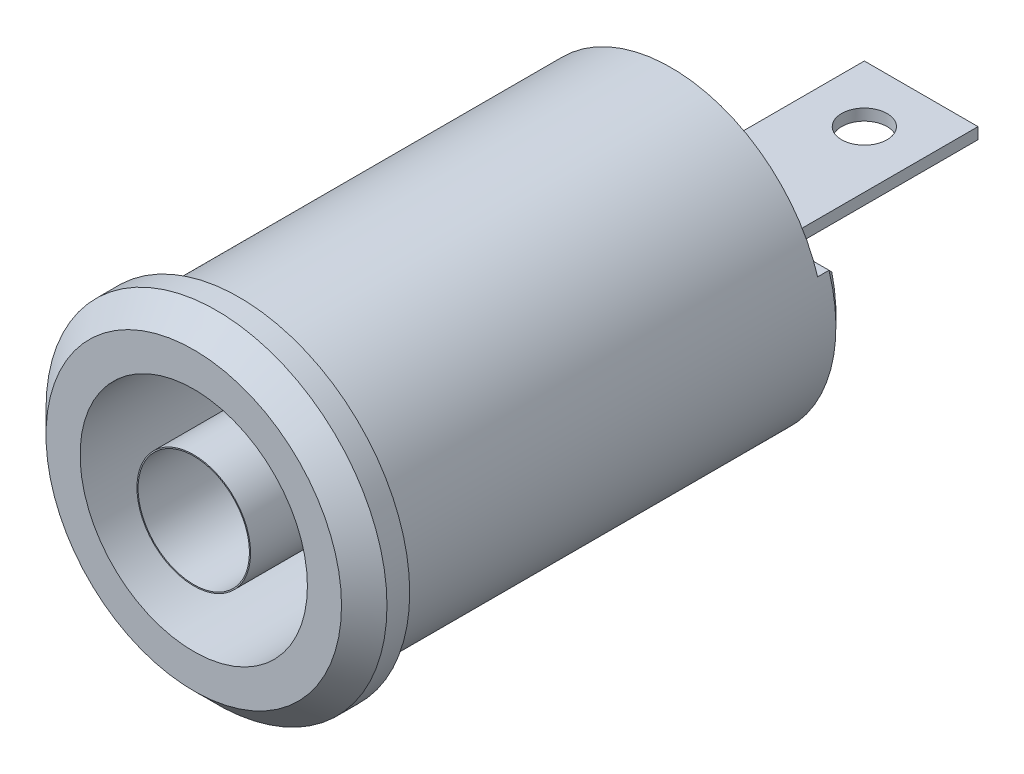
SolidWorks part; units mm, degrees
ref_plane "Plan de face" through (0, 0, 0) normal (0, 0, 1) x (1, 0, 0)
ref_plane "Plan de dessus" through (0, 0, 0) normal (0, 1, 0) x (1, 0, 0)
ref_plane "Plan de droite" through (0, 0, 0) normal (1, 0, 0) x (0, 0, -1)
sketch "Esquisse1" plane through (0, 0, 0) normal (0, 0, 1) x (1, 0, 0)
  circle A0 centre (0, 0) radius 7.5
  dimension "D1" = 15
extrude "Extrusion1" add sketch "Esquisse1" against normal blind 32
sketch "Esquisse2" plane through (0, 0, 0) normal (0, 0, 1) x (1, 0, 0)
  circle A0 centre (0, 0) radius 5
  circle A1 centre (0, 0) radius 2.5
  circle A2 centre (0, 0) radius 2.45
  dimension "D1" = 10
  dimension "D2" = 5
  dimension "D3" = 4.9
extrude "Extrusion3" cut sketch "Esquisse2" against normal blind 18 contours A0 A1 | A2
sketch "Esquisse3" plane through (0, 0, -32) normal (0, 0, -1) x (-1, 0, 0)
  circle A0 centre (0, 0) radius 6.75
  dimension "D1" = 13.5
extrude "Extrusion5" cut sketch "Esquisse3" against normal blind 30 flip side to cut
sketch "Esquisse4" plane through (0, 0, -32) normal (0, 0, -1) x (-1, 0, 0)
  line L0 (0, 7.9888) -> (0, -8.2444) construction
  line L1 (-2.5, 0.25) -> (2.5, 0.25)
  line L2 (-2.5, 0.25) -> (-2.5, -0.25)
  line L3 (-2.5, -0.25) -> (2.5, -0.25)
  line L4 (2.5, 0.25) -> (2.5, -0.25)
  line L5 (9.1392, 0) -> (-9.0881, 0) construction
  dimension "D1" = 0.25
  dimension "D2" = 0.25
  dimension "D3" = 2.5
  dimension "D4" = 2.5
extrude "Extrusion6" cut sketch "Esquisse4" against normal blind 10 flip side to cut
sketch "Esquisse5" plane through (0, 0, -22) normal (0, 0, -1) x (-1, 0, 0)
  line L0 (0, 8.1678) -> (0, -8.6023) construction
  line L1 (-9, 8) -> (9, 8)
  line L2 (-9, 8) -> (-9, 2)
  line L3 (-9, 2) -> (9, 2)
  line L4 (9, 8) -> (9, 2)
  line L5 (-11.3121, 0) -> (10.443, 0) construction
  dimension "D1" = 2
  dimension "D2" = 18
  dimension "D3" = 9
  dimension "D4" = 6
extrude "Extrusion7" cut sketch "Esquisse5" against normal blind 1
sketch "Esquisse6" plane through (0, 0.25, 0) normal (0, 1, 0) x (1, 0, 0)
  line L0 (-2.5, 22) -> (-2.5, 32) construction
  line L2 (-2.5, 32) -> (2.5, 32) construction
  circle A0 centre (0, 29.5) radius 1
  dimension "D1" = 2
  dimension "D2" = 2.5
  dimension "D3" = 2.5
extrude "Extrusion8" cut sketch "Esquisse6" against normal through all
chamfer "Chanfrein1" distance 1 angle 45 1 edges at (7.5, 0, 0)
chamfer "Chanfrein2" distance 0.5 angle 45 2 edges at (0, -6.75, -22) (0, 2, -22)
